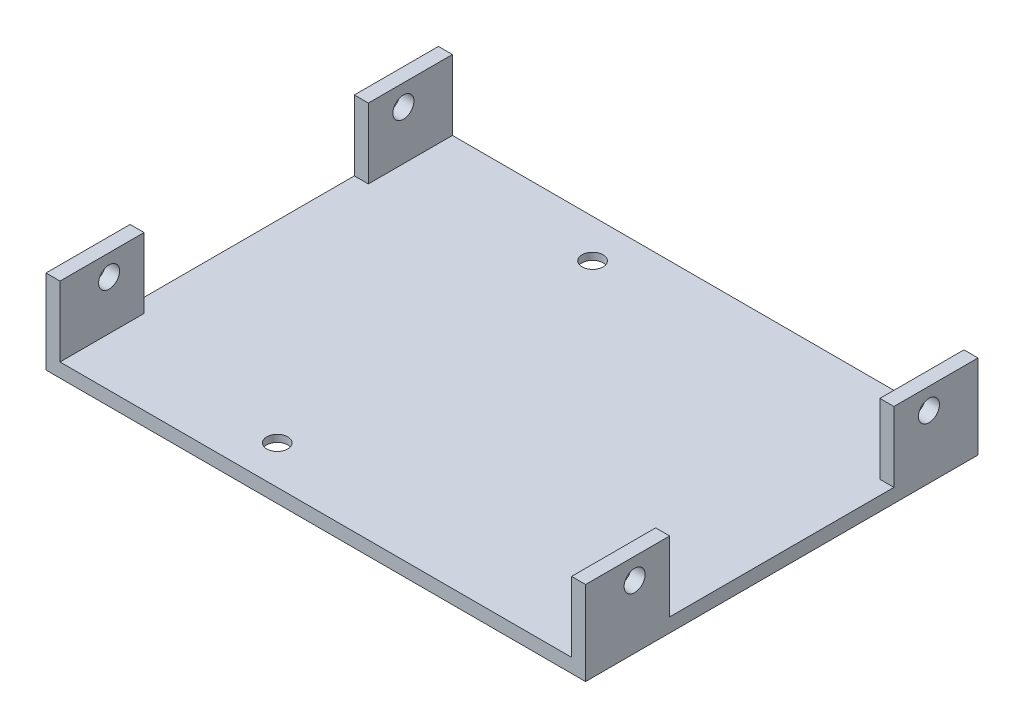
SolidWorks part; units mm, degrees
ref_plane "Front Plane" through (0, 0, 0) normal (0, 0, 1) x (1, 0, 0)
ref_plane "Top Plane" through (0, 0, 0) normal (0, 1, 0) x (1, 0, 0)
ref_plane "Right Plane" through (0, 0, 0) normal (1, 0, 0) x (0, 0, -1)
sketch "Sketch1" plane through (0, 0, 0) normal (0, 1, 0) x (1, 0, 0)
  line L1 (-41.6205, 21.9093) -> (35.3795, 21.9093)
  line L2 (-41.6205, 21.9093) -> (-41.6205, -34.0907)
  line L3 (-41.6205, -34.0907) -> (35.3795, -34.0907)
  line L4 (35.3795, 21.9093) -> (35.3795, -34.0907)
  dimension "D1" = 77
  dimension "D2" = 56
extrude "Boss-Extrude1" add sketch "Sketch1" along normal blind 2
sketch "Sketch2" plane through (0, 2, 0) normal (0, 1, 0) x (1, 0, 0)
  line L0 (35.3795, -34.0907) -> (35.3795, 21.9093) construction
  line L1 (-41.6205, -34.0907) -> (35.3795, -34.0907) construction
  circle A1 centre (30.8795, 16.4093) radius 1.5
  circle A2 centre (30.8795, -28.5907) radius 1.5
  circle A3 centre (-14.1205, 16.4093) radius 1.5
  circle A4 centre (-14.1205, -28.5907) radius 1.5
  point P0 (0, 0)
  dimension "D3" = 45
  dimension "D8" = 5.5
  dimension "D9" = 3
  dimension "D10" = 3
  dimension "D11" = 3
  dimension "D12" = 3
  dimension "D1" = 45
  dimension "D2" = 45
  dimension "D4" = 45
  dimension "D5" = 4.5
  dimension "D6" = 4.5
  dimension "D7" = 5.5
extrude "Cut-Extrude1" cut sketch "Sketch2" against normal through all
sketch "Sketch3" plane through (0, 2, 0) normal (0, 1, 0) x (1, 0, 0)
  line L0 (35.3795, -34.0907) -> (35.3795, 21.9093) construction
  line L1 (33.3795, 21.9093) -> (35.3795, 21.9093)
  line L2 (33.3795, 21.9093) -> (33.3795, 9.9093)
  line L3 (33.3795, 9.9093) -> (35.3795, 9.9093)
  line L4 (35.3795, 21.9093) -> (35.3795, 9.9093)
  line L5 (33.3795, -22.0907) -> (35.3795, -22.0907)
  line L6 (33.3795, -22.0907) -> (33.3795, -34.0907)
  line L7 (33.3795, -34.0907) -> (35.3795, -34.0907)
  line L8 (35.3795, -22.0907) -> (35.3795, -34.0907)
  line L9 (-41.6205, 21.9093) -> (-39.6205, 21.9093)
  line L10 (-41.6205, 21.9093) -> (-41.6205, 9.9093)
  line L11 (-41.6205, 9.9093) -> (-39.6205, 9.9093)
  line L12 (-39.6205, 21.9093) -> (-39.6205, 9.9093)
  line L13 (-41.6205, -22.0907) -> (-39.6205, -22.0907)
  line L14 (-41.6205, -22.0907) -> (-41.6205, -34.0907)
  line L15 (-41.6205, -34.0907) -> (-39.6205, -34.0907)
  line L16 (-39.6205, -22.0907) -> (-39.6205, -34.0907)
  line L17 (35.3795, 21.9093) -> (-41.6205, 21.9093) construction
  line L18 (35.3795, -34.0907) -> (35.3795, 21.9093) construction
  line L19 (-41.6205, -34.0907) -> (35.3795, -34.0907) construction
  line L20 (-41.6205, 21.9093) -> (-41.6205, -34.0907) construction
  dimension "D1" = 2
  dimension "D2" = 2
  dimension "D3" = 12
  dimension "D4" = 12
  dimension "D5" = 2
  dimension "D6" = 12
  dimension "D7" = 2
  dimension "D8" = 12
  dimension "D9" = 0
  dimension "D10" = 0
  dimension "D11" = 0
  dimension "D12" = 0
  dimension "D13" = 0
  dimension "D14" = 0
  dimension "D15" = 0
  dimension "D16" = 0
extrude "Boss-Extrude2" add sketch "Sketch3" along normal blind 10
sketch "Sketch4" plane through (35.3795, 0, 0) normal (1, 0, 0) x (0, 0, -1)
  line L1 (-22.0907, 2) -> (9.9093, 2) construction
  line L2 (21.9093, 12) -> (21.9093, 0) construction
  circle A2 centre (-27.0907, 9) radius 1.5
  circle A3 centre (14.9093, 9) radius 1.5
  dimension "D2" = 3
  dimension "D3" = 3
  dimension "D1" = 42
  dimension "D4" = 7
  dimension "D5" = 7
  dimension "D6" = 7
extrude "Cut-Extrude2" cut sketch "Sketch4" against normal through all
sketch "Sketch5" plane through (0, 0, 0) normal (0, -1, 0) x (-1, 0, 0)
  circle A0 centre (14.1205, -28.5907) radius 3.25
  circle A1 centre (-30.8795, -28.5907) radius 3.25
  circle A2 centre (-30.8795, 16.4093) radius 3.25
  circle A3 centre (14.1205, 16.4093) radius 3.25
  circle A4 centre (14.1205, -28.5907) radius 1.5 construction
  circle A5 centre (-30.8795, -28.5907) radius 1.5 construction
  circle A6 centre (-30.8795, 16.4093) radius 1.5 construction
  circle A7 centre (14.1205, 16.4093) radius 1.5 construction
  dimension "D1" = 6.5
  dimension "D2" = 6.5
  dimension "D3" = 6.5
  dimension "D4" = 6.5
extrude "Cut-Extrude3" cut sketch "Sketch5" against normal blind 1
